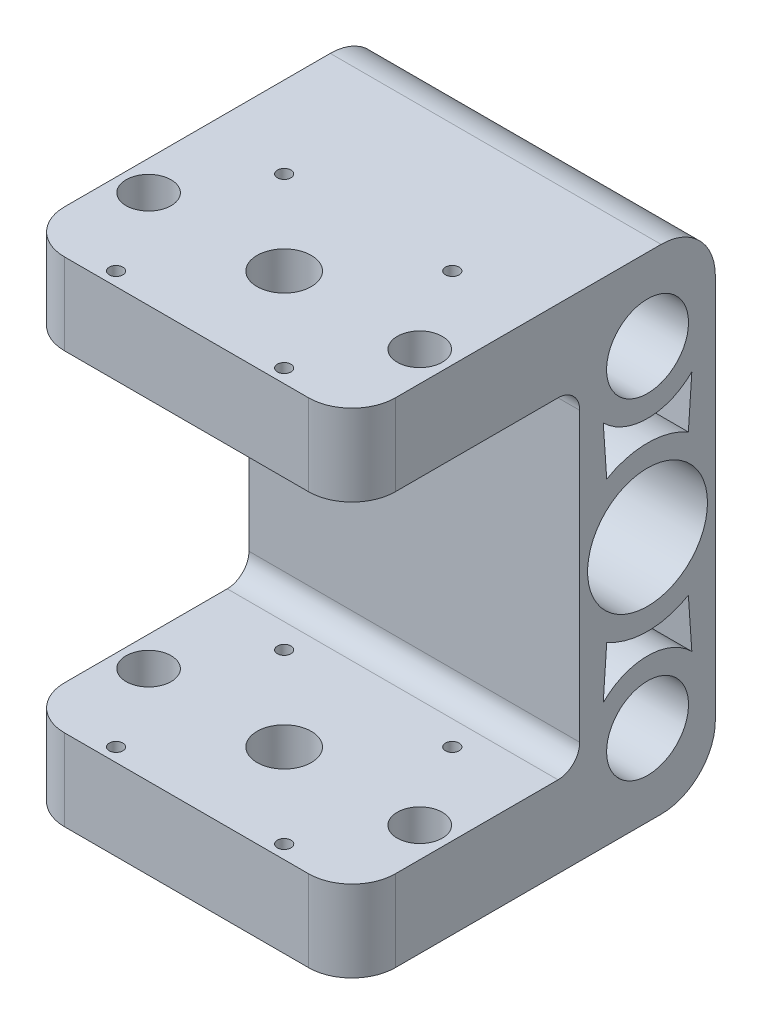
SolidWorks part; units mm, degrees
ref_plane "Alzado" through (0, 0, 0) normal (0, 0, 1) x (1, 0, 0)
ref_plane "Planta" through (0, 0, 0) normal (0, 1, 0) x (1, 0, 0)
ref_plane "Vista lateral" through (0, 0, 0) normal (1, 0, 0) x (0, 0, -1)
sketch "Sketch1" plane through (0, 0, 0) normal (1, 0, 0) x (0, 0, -1)
  line L0 (0, 15.5) -> (0, -15.5)
  line L1 (0, 15.5) -> (-42, 15.5)
  line L2 (-42, 15.5) -> (-42, 45.5)
  line L3 (-42, 45.5) -> (15, 45.5)
  line L4 (25, 35.5) -> (25, -35.5)
  line L5 (0, 12.3265) -> (0, -13.9278) construction
  line L6 (-12.3179, 0) -> (23.889, 0) construction
  line L7 (12.5, 70.0436) -> (12.5, -9.0436) construction
  line L8 (3.1279, 30.5) -> (22.5369, 30.5) construction
  line L9 (-42, -45.5) -> (15, -45.5)
  line L10 (-42, -15.5) -> (-42, -45.5)
  line L11 (0, -15.5) -> (-42, -15.5)
  circle A0 centre (12.5, 0) radius 5.05
  circle A1 centre (12.5, 30.5) radius 7.55
  circle A2 centre (12.5, -30.5) radius 7.55
  arc A3 (15, -45.5) -> (25, -35.5) centre (15, -35.5) ccw
  arc A4 (15, 45.5) -> (25, 35.5) centre (15, 35.5) cw
  point P13 (25, 0)
  point P27 (0, 0)
  point P29 (25, -45.5)
  point P32 (25, 45.5)
  dimension "D2" = 15.1
  dimension "D5" = 10.1
  dimension "D7" = 10
  dimension "D1" = 25
  dimension "D3" = 30
  dimension "D4" = 30.5
  dimension "D6" = 42
extrude "Boss-Extrude1" add sketch "Sketch1" along normal mid plane 61
sketch "Sketch2" plane through (0, 0, 0) normal (0, 1, 0) x (1, 0, 0)
  line L0 (0, -30.056) -> (0, 7.2447) construction
  line L1 (30.5, -42) -> (-30.5, -42) construction
  circle A0 centre (0, -24) radius 5
  circle A1 centre (25, -24) radius 4.15
  circle A2 centre (-25, -24) radius 4.15
  circle A3 centre (15.5, -39.5) radius 1.25
  circle A4 centre (-15.5, -39.5) radius 1.25
  circle A5 centre (-15.5, -8.5) radius 1.25
  circle A6 centre (15.5, -8.5) radius 1.25
  dimension "D3" = 10
  dimension "D4" = 8.3
  dimension "D5" = 2.5
  dimension "D1" = 25
  dimension "D2" = 18
  dimension "D6" = 15.5
  dimension "D7" = 15.5
  dimension "D10" = 15.5
  dimension "D11" = 15.5
  dimension "D12" = 15.5
  dimension "D8" = 2
  dimension "D9" = 2
extrude "Cut-Extrude1" cut sketch "Sketch2" along normal up to surface and the other way up to surface up to face at (0, 45.5, 13.5) other way up to face at (0, -45.5, 13.5)
sketch "Croquis1" plane through (30.5, 0, 0) normal (1, 0, 0) x (0, 0, -1)
  line L0 (12.5, 38.05) -> (12.5, -38.05) construction
  line L1 (5.5314, 0) -> (9.0157, -6.035)
  line L2 (9.0157, -6.035) -> (15.9843, -6.035)
  line L3 (15.9843, -6.035) -> (19.4686, 0)
  line L4 (19.4686, 0) -> (15.9843, 6.035)
  line L5 (15.9843, 6.035) -> (9.0157, 6.035)
  line L6 (9.0157, 6.035) -> (5.5314, 0)
  circle A0 centre (12.5, 0) radius 6.035 construction
  circle A1 centre (12.5, 30.5) radius 7.55 construction
  circle A2 centre (12.5, -30.5) radius 7.55 construction
  circle A3 centre (12.5, 0) radius 5.05 construction
  circle A4 centre (12.5, 0) radius 5.05
  dimension "D1" = 12.07
sketch "Croquis4" plane through (30.5, 0, 0) normal (1, 0, 0) x (0, 0, -1)
  line L0 (-42, 45.5) -> (-42, 15.5) construction
  line L1 (0, -30.5) -> (-42, -30.5)
  line L2 (0, -30.5) -> (0, 30.5)
  line L3 (0, 30.5) -> (-42, 30.5)
  line L4 (-42, -30.5) -> (-42, 30.5)
  line L5 (0, -30.5) -> (-42, 30.5) construction
  line L6 (0, 30.5) -> (-42, -30.5) construction
  line L7 (0, 15.5) -> (0, -15.5) construction
  line L8 (-42, 15.5) -> (0, 15.5) construction
  line L9 (0, -15.5) -> (-42, -15.5) construction
  point P0 (-21, 0)
  dimension "D1" = 15
  dimension "D2" = 15
extrude "Cortar-Extruir1" cut sketch "Croquis4" against normal through all
fillet "Redondeo4" radius 4 2 edges at (0, -30.5, 0) (0, 30.5, 0)
fillet "Redondeo5" radius 8 4 edges at (-30.5, 38, 42) (-30.5, -38, 42) (30.5, -38, 42) (30.5, 38, 42)
sketch "Croquis5" plane through (30.5, 0, 0) normal (1, 0, 0) x (0, 0, -1)
  circle A1 centre (12.5, 0) radius 11.05
  dimension "D1" = 22.1
extrude "Cortar-Extruir2" cut sketch "Croquis5" against normal blind 20
sketch "Croquis6" plane through (10.5, 0, 0) normal (1, 0, 0) x (0, 0, -1)
  line L0 (12.5, 38.05) -> (12.5, -38.05) construction
  circle A0 centre (12.5, 8) radius 1.25
  circle A1 centre (20.5, 0) radius 1.25
  circle A2 centre (12.5, -8) radius 1.25
  circle A3 centre (4.5, 0) radius 1.25
  point P14 (12.5, 0)
  dimension "D1" = 2.5
  dimension "D2" = 8
  dimension "D4" = 8
  dimension "D3" = 4
extrude "Cortar-Extruir3" cut sketch "Croquis6" against normal through all
sketch "Croquis8" plane through (30.5, 0, 0) normal (1, 0, 0) x (0, 0, -1)
  line L0 (4.3329, 22.3329) -> (12.5, 30.5) construction
  line L1 (12.5, 30.5) -> (20.6671, 22.3329) construction
  line L2 (12.5, 34.9103) -> (12.5, -2.5117) construction
  line L3 (4.975, 13.0337) -> (12.5, 0) construction
  line L4 (12.5, 0) -> (20.025, 13.0337) construction
  line L7 (-40.8658, 0) -> (40.8658, 0) construction
  line L8 (4.3329, 22.3329) -> (4.975, 13.0337)
  line L9 (20.6671, 22.3329) -> (20.025, 13.0337)
  line L10 (4.3329, -22.3329) -> (4.975, -13.0337)
  line L11 (20.6671, -22.3329) -> (20.025, -13.0337)
  arc A0 (4.3329, 22.3329) -> (20.6671, 22.3329) centre (12.5, 30.5) ccw
  circle A1 centre (12.5, 30.5) radius 7.55 construction
  arc A3 (4.975, 13.0337) -> (20.025, 13.0337) centre (12.5, 0) cw
  circle A5 centre (12.5, 0) radius 11.05 construction
  arc A6 (4.3329, -22.3329) -> (20.6671, -22.3329) centre (12.5, -30.5) cw
  arc A7 (4.975, -13.0337) -> (20.025, -13.0337) centre (12.5, 0) ccw
  dimension "D1" = 90
  dimension "D2" = 4
  dimension "D3" = 60
  dimension "D4" = 4
extrude "Cortar-Extruir4" cut sketch "Croquis8" against normal up to surface (61 mm away) up to face at (-30.5, 8, -13.75)
